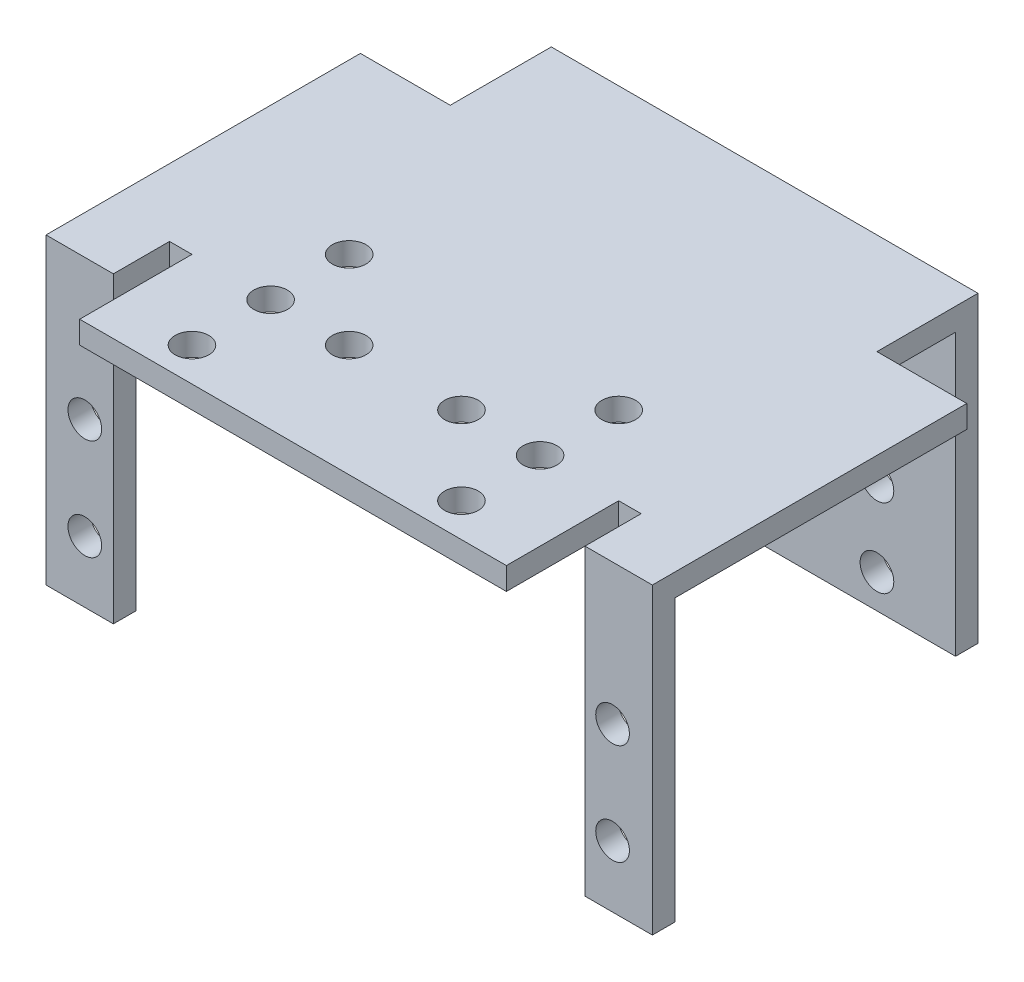
SolidWorks part; units mm, degrees
ref_plane "Front Plane" through (0, 0, 0) normal (0, 0, 1) x (1, 0, 0)
ref_plane "Top Plane" through (0, 0, 0) normal (0, 1, 0) x (1, 0, 0)
ref_plane "Right Plane" through (0, 0, 0) normal (1, 0, 0) x (0, 0, -1)
sketch "Sketch1" plane through (0, 0, 0) normal (0, 0, 1) x (1, 0, 0)
  line L1 (0, 0) -> (19, 0)
  line L2 (0, 0) -> (0, 27)
  line L3 (0, 27) -> (19, 27)
  line L4 (19, 0) -> (19, 27)
  dimension "D1" = 27
  dimension "D2" = 19
extrude "Boss-Extrude1" add sketch "Sketch1" along normal blind 2
sketch "Sketch2" plane through (0, 0, 2) normal (0, 0, 1) x (1, 0, 0)
  line L0 (19, 0) -> (19, 27) construction
  line L1 (0, 27) -> (19, 27)
  line L2 (0, 27) -> (0, 25)
  line L3 (0, 25) -> (19, 25)
  line L4 (19, 27) -> (19, 25)
  dimension "D1" = 2
extrude "Boss-Extrude2" add sketch "Sketch2" along normal blind 40
sketch "Sketch3" plane through (0, 25, 0) normal (0, -1, 0) x (-1, 0, 0)
  line L0 (-19, -42) -> (-19, -2) construction
  line L1 (-19, -9) -> (-27, -9)
  line L2 (-19, -9) -> (-19, -34)
  line L3 (-21, -37) -> (-27, -37)
  line L4 (-27, -9) -> (-27, -37)
  line L5 (0, -2) -> (-19, -2) construction
  line L6 (0, -42) -> (-19, -42) construction
  line L9 (-19, -34) -> (-19, -32)
  line L10 (-19, -32) -> (-21, -32)
  line L11 (-21, -37) -> (-21, -32)
  line M6 (-19, -2) -> (-19, -42)
  dimension "D1" = 8
  dimension "D2" = 7
  dimension "D3" = 5
  dimension "D4" = 5
  dimension "D5" = 2
extrude "Boss-Extrude3" add sketch "Sketch3" against normal blind 2 contours L3 L11 L10 L1 L4 M6
sketch "Sketch5" plane through (0, 25, 0) normal (0, -1, 0) x (-1, 0, 0)
  line L0 (-27, -9) -> (-27, -37) construction
  line L1 (-21, -37) -> (-27, -37)
  line L2 (-21, -37) -> (-21, -35)
  line L3 (-21, -35) -> (-27, -35)
  line L4 (-27, -37) -> (-27, -35)
  dimension "D1" = 2
extrude "Boss-Extrude4" add sketch "Sketch5" along normal blind 25
sketch "Sketch6" plane through (0, 0, 2) normal (0, 0, 1) x (1, 0, 0)
  line L0 (19, 0) -> (19, 27) construction
  line L1 (0, 0) -> (19, 0) construction
  circle A0 centre (12, 3) radius 1.5
  circle A1 centre (12, 10) radius 1.5
  circle A2 centre (12, 17) radius 1.5
  circle A4 centre (5, 10) radius 1.5
  dimension "D1" = 3
  dimension "D2" = 3
  dimension "D3" = 3
  dimension "D7" = 3
  dimension "D11" = 7
  dimension "D4" = 3
  dimension "D5" = 7
  dimension "D6" = 7
  dimension "D10" = 7
extrude "Cut-Extrude1" cut sketch "Sketch6" against normal up to next (2 mm away)
mirror "Mirror2" about plane through (0, 0, 2) normal (1, 0, 0) of "Boss-Extrude4", "Boss-Extrude3", "Boss-Extrude2", "Boss-Extrude1", "Cut-Extrude1"
sketch "Sketch7" plane through (0, 0, 35) normal (0, 0, -1) x (-1, 0, 0)
  circle A0 centre (-23.4563, 5.5) radius 1.5
  circle A1 centre (-23.4563, 14.5) radius 1.5
  circle A2 centre (23.5437, 5.5) radius 1.5
  circle A3 centre (23.5437, 14.5) radius 1.5
  dimension "D1" = 3
  dimension "D2" = 3
  dimension "D3" = 3
  dimension "D4" = 3
extrude "Cut-Extrude2" cut sketch "Sketch7" against normal up to next
sketch "Sketch9" plane through (0, 27, 0) normal (0, 1, 0) x (1, 0, 0)
  circle A0 centre (12, -32) radius 1.5
  circle A1 centre (12, -25) radius 1.5
  circle A2 centre (12, -39) radius 1.5
  circle A3 centre (5, -32) radius 1.5
  circle A4 centre (-5, -32) radius 1.5
  circle A5 centre (-12, -32) radius 1.5
  circle A6 centre (-12, -39) radius 1.5
  circle A7 centre (-12, -25) radius 1.5
  dimension "D1" = 3
  dimension "D2" = 3
  dimension "D3" = 3
  dimension "D4" = 3
  dimension "D5" = 3
  dimension "D6" = 3
  dimension "D7" = 3
  dimension "D8" = 3
extrude "Cut-Extrude4" cut sketch "Sketch9" against normal up to next
